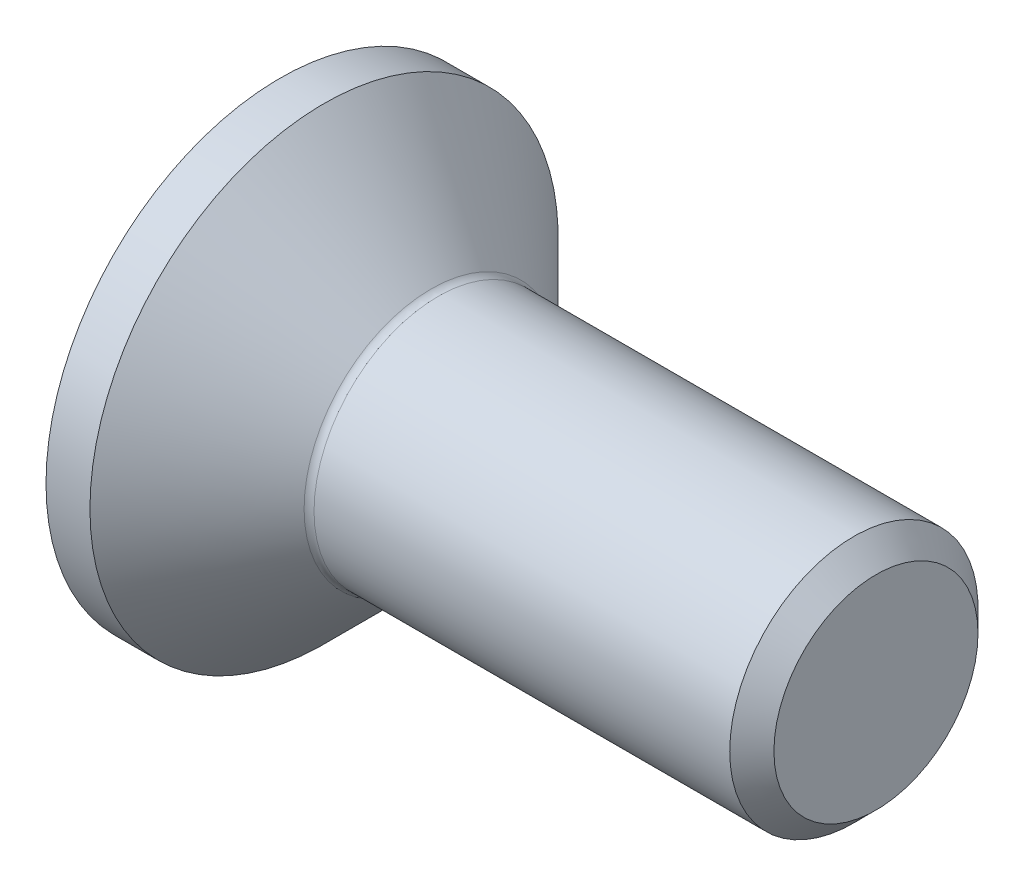
SolidWorks part; units mm, degrees
ref_plane "Plane1" through (0, 0, 0) normal (0, 0, 1) x (1, 0, 0)
ref_plane "Plane2" through (0, 0, 0) normal (0, 1, 0) x (1, 0, 0)
ref_plane "Plane3" through (0, 0, 0) normal (1, 0, 0) x (0, 0, -1)
sketch "BodySke" plane through (0, 0, 0) normal (0, 0, 1) x (1, 0, 0)
  line L0 (0, 0) -> (0, 4.715)
  line L1 (0.885, 4.715) -> (3.1, 2.5)
  line L2 (0, 4.715) -> (0.885, 4.715)
  line L3 (3.1, 2.5) -> (11.555, 2.5)
  line L4 (12, 2.055) -> (12, 0)
  line L5 (12, 0) -> (0, 0)
  line L6 (0, 0) -> (127, 0) construction
  line L7 (0.885, -4.715) -> (3.1, -2.5) construction
  line L8 (12, 2.055) -> (11.555, 2.5)
  line L9 (0, -4.715) -> (0.885, -4.715) construction
  line L10 (12, -2.055) -> (11.555, -2.5) construction
  line L11 (3.9, 8.85) -> (3.9, -13.375) construction
  line L12 (0, 19.05) -> (0, -3.175) construction
  dimension "D1" = 0.885
  dimension "Diameter" = 5
  dimension "Head_ht" = 3.1
  dimension "Length" = 12
  dimension "Body_ch_ang" = 45
  dimension "Head_dia" = 9.43
  dimension "Minor_dia" = 4.11
  dimension "Head_ang" = 90
  dimension "Advance" = 0.8
  dimension "Thread_nom" = 12
revolve "BaseBody" add sketch "BodySke"
cosmetic thread "ThreadCosmetic"
fillet "Fillet1" radius 0.2 1 edges at (3.1, 0, 2.5)
sketch "Sketch2" plane through (0, 0, 0) normal (0, 0, 1) x (1, 0, 0)
  line L0 (0, 1.5) -> (1.9, 1.5)
  line L1 (1.9, 1.5) -> (2.766, 0)
  line L2 (0, 0) -> (127, 0) construction
  line L3 (2.766, 0) -> (0, 0)
  line L4 (0, 0) -> (0, 1.5)
  line L5 (0, -1.5) -> (1.9, -1.5) construction
  line L6 (0, 0) -> (47.625, 0) construction
  line L8 (0, 4.715) -> (0, -4.715) construction
  dimension "D2" = 60
  dimension "PreBroach_depth" = 1.9
  dimension "PreBroach_dia" = 3
revolve "PreBroach" cut sketch "Sketch2" angle 360 about L6
sketch "Sketch3" plane through (0, 0, 0) normal (-1, 0, 0) x (0, 0, 1)
  line L0 (-1.5, -0.866) -> (-1.5, 0.866)
  line L1 (-1.5, 0.866) -> (0, 1.7321)
  line L2 (0, 1.7321) -> (1.5, 0.866)
  line L3 (1.5, 0.866) -> (1.5, -0.866)
  line L4 (1.5, -0.866) -> (0, -1.7321)
  line L5 (0, -1.7321) -> (-1.5, -0.866)
  dimension "D1" = 1.5
  dimension "D2" = 1.5
  dimension "D3" = 3
  dimension "Hex_size" = 3
extrude "Hex" cut sketch "Sketch3" against normal blind 1.9
sketch "ThdSchSke" plane through (0, 0, 0) normal (0, 0, 1) x (1, 0, 0)
  line L0 (5.5, -2.055) -> (5.1884, -2.5)
  line L1 (5.5, -2.055) -> (5.8116, -2.5)
  line L2 (5.8116, -2.5) -> (5.8116, -3.125)
  line L3 (-3.175, 0) -> (5.1513, 0) construction
  line L4 (0, 4.715) -> (0, -4.715) construction
  line L5 (5.8116, -3.125) -> (5.1884, -3.125)
  line L6 (5.1884, -3.125) -> (5.1884, -2.5)
  dimension "Thread_minor" = 4.11
  dimension "Diameter" = 5
  dimension "Start" = 5.5
  dimension "SideAngle" = 55
  dimension "VeeAngle" = 70
  dimension "Overcut" = 6.25
revolve "ThreadSchematic" [suppressed] cut sketch "ThdSchSke" angle 360 about L3
pattern_linear "ThdSchPat" [suppressed]
equation "\"Thread_minor@ThreadCosmetic\"  =  \"Minor_dia@BodySke\""
equation "\"D1@Sketch3\" = \"Hex_size@Sketch3\" / 2"
equation "\"D2@Sketch3\" = \"D1@Sketch3\""
equation "\"D3@Sketch3\" = \"Hex_size@Sketch3\""
equation "\"Thread_length@ThreadCosmetic\" = ((sgn( (\"Length@BodySke\" - \"Advance@BodySke\" * 3.0 - \"Head_ht@BodySke\" ) - \"Thread_nom@BodySke\" )-1)*( (\"Length@BodySke\" - \"Advance@BodySke\" * 3.0 - \"Head_ht@BodySke\" ) - \"Thread_nom@BodySke\" ))/-2+ \"Thread_nom@BodySke\""
equation "\"Thread_minor@ThdSchSke\" = \"Minor_dia@BodySke\""
equation "\"Diameter@ThdSchSke\" = \"Diameter@BodySke\""
equation "\"Overcut@ThdSchSke\" = \"Diameter@BodySke\" * 1.25"
equation "\"Start@ThdSchSke\" = 0.000001 + \"Length@BodySke\" - \"Thread_length@ThreadCosmetic\"  '---Countersunk---"
equation "\"Num_threads@ThdSchPat\" = int( \"Thread_length@ThreadCosmetic\" / \"Advance@BodySke\" + 0.999 )  + 1"
equation "\"Advance@ThdSchPat\" = \"Thread_length@ThreadCosmetic\" /  (\"Num_threads@ThdSchPat\" - 1) 'relax it"
equation "\"Num_threads@ThdSchPat\" = \"Num_threads@ThdSchPat\" - sgn( \"Num_threads@ThdSchPat\" - 1) '---chamfered tips only---"
